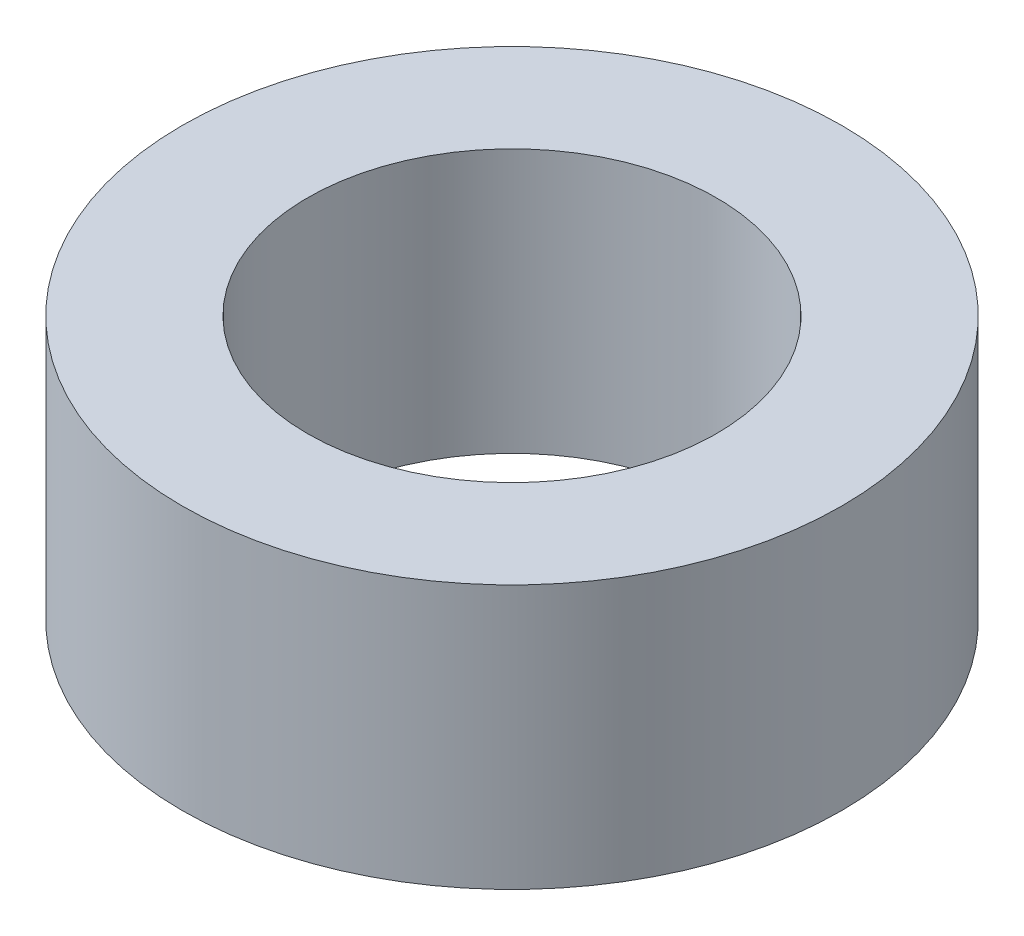
SolidWorks part; units mm, degrees
material "6061 合金"
ref_plane "前视基准面" through (0, 0, 0) normal (0, 0, 1) x (1, 0, 0)
ref_plane "上视基准面" through (0, 0, 0) normal (0, 1, 0) x (1, 0, 0)
ref_plane "右视基准面" through (0, 0, 0) normal (1, 0, 0) x (0, 0, -1)
sketch "草图1" plane through (0, 0, 0) normal (0, 1, 0) x (1, 0, 0)
  circle A0 centre (0, 0) radius 1.55
  circle A1 centre (0, 0) radius 2.5
  dimension "D1" = 5
  dimension "D2" = 3.1
extrude "凸台-拉伸1" add sketch "草图1" along normal blind 2
